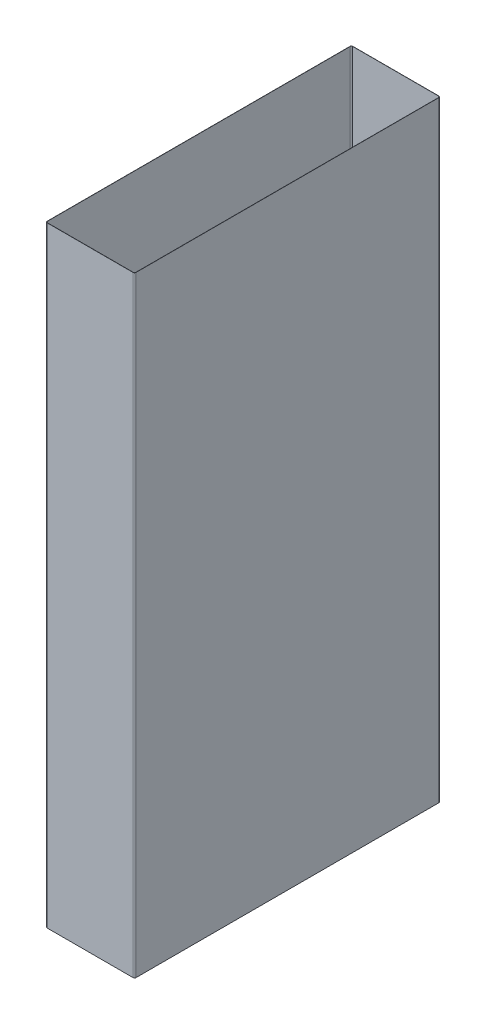
SolidWorks part; units mm, degrees
ref_plane "Front" through (0, 0, 0) normal (0, 0, 1) x (1, 0, 0)
ref_plane "Top" through (0, 0, 0) normal (0, 1, 0) x (1, 0, 0)
ref_plane "Right" through (0, 0, 0) normal (1, 0, 0) x (0, 0, -1)
sketch "Sketch1" plane through (0, 0, 0) normal (0, 1, 0) x (1, 0, 0)
  line L1 (1, 0) -> (69.2, 0)
  line L2 (0, 1) -> (0, 241.4)
  line L3 (1, 242.4) -> (69.2, 242.4)
  line L4 (70.2, 1) -> (70.2, 241.4)
  arc A0 (1, 0) -> (0, 1) centre (1, 1) cw
  arc A1 (69.2, 0) -> (70.2, 1) centre (69.2, 1) ccw
  arc A2 (69.2, 242.4) -> (70.2, 241.4) centre (69.2, 241.4) cw
  arc A3 (0, 241.4) -> (1, 242.4) centre (1, 241.4) cw
  point P7 (0, 0)
  point P10 (70.2, 0)
  point P15 (0, 242.4)
  dimension "D3" = 1
  dimension "D1" = 242.4
  dimension "D2" = 70.2
extrude "Extrude-Thin1" add sketch "Sketch1" along normal blind 484.8 thin
